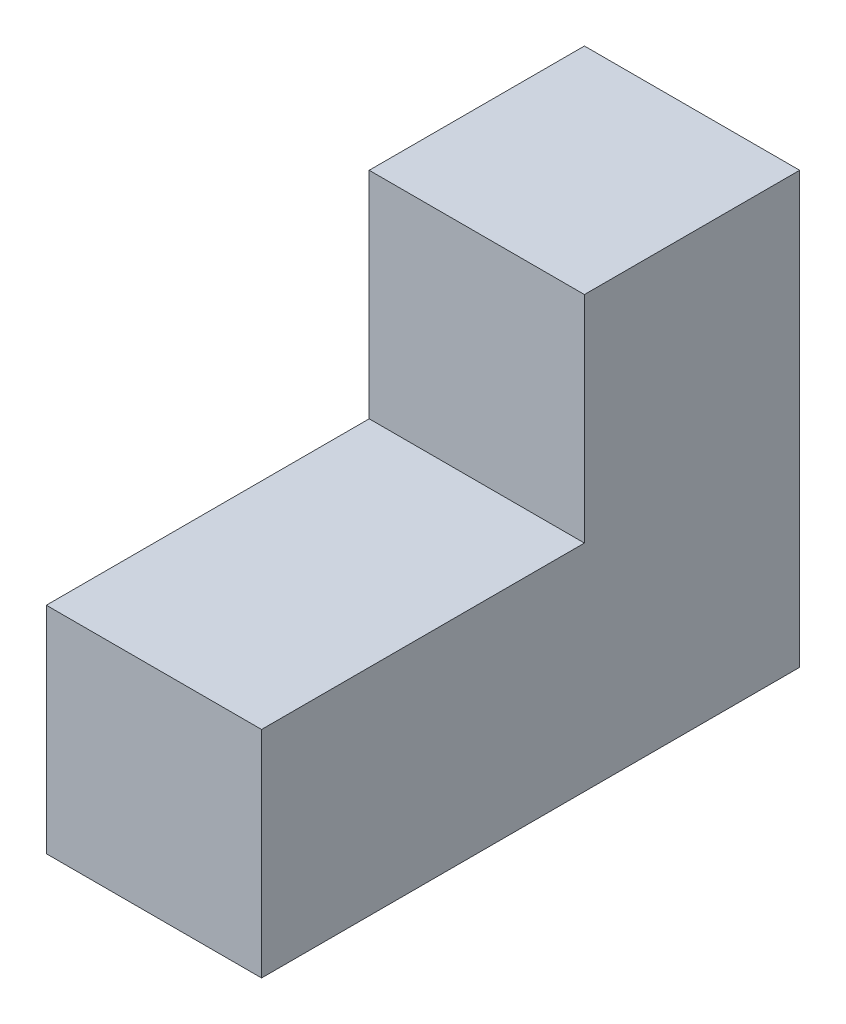
SolidWorks part; units mm, degrees
ref_plane "Front Plane" through (0, 0, 0) normal (0, 0, 1) x (1, 0, 0)
ref_plane "Top Plane" through (0, 0, 0) normal (0, 1, 0) x (1, 0, 0)
ref_plane "Right Plane" through (0, 0, 0) normal (1, 0, 0) x (0, 0, -1)
sketch "Sketch1" plane through (0, 0, 0) normal (1, 0, 0) x (0, 0, -1)
  line L0 (0, 0) -> (50, 0)
  line L1 (50, 0) -> (50, 40)
  line L2 (50, 40) -> (30, 40)
  line L3 (30, 40) -> (30, 20)
  line L4 (30, 20) -> (0, 20)
  line L5 (0, 20) -> (0, 0)
  dimension "D1" = 50
  dimension "D2" = 40
  dimension "D3" = 30
  dimension "D4" = 20
extrude "Boss-Extrude1" add sketch "Sketch1" along normal blind 20
